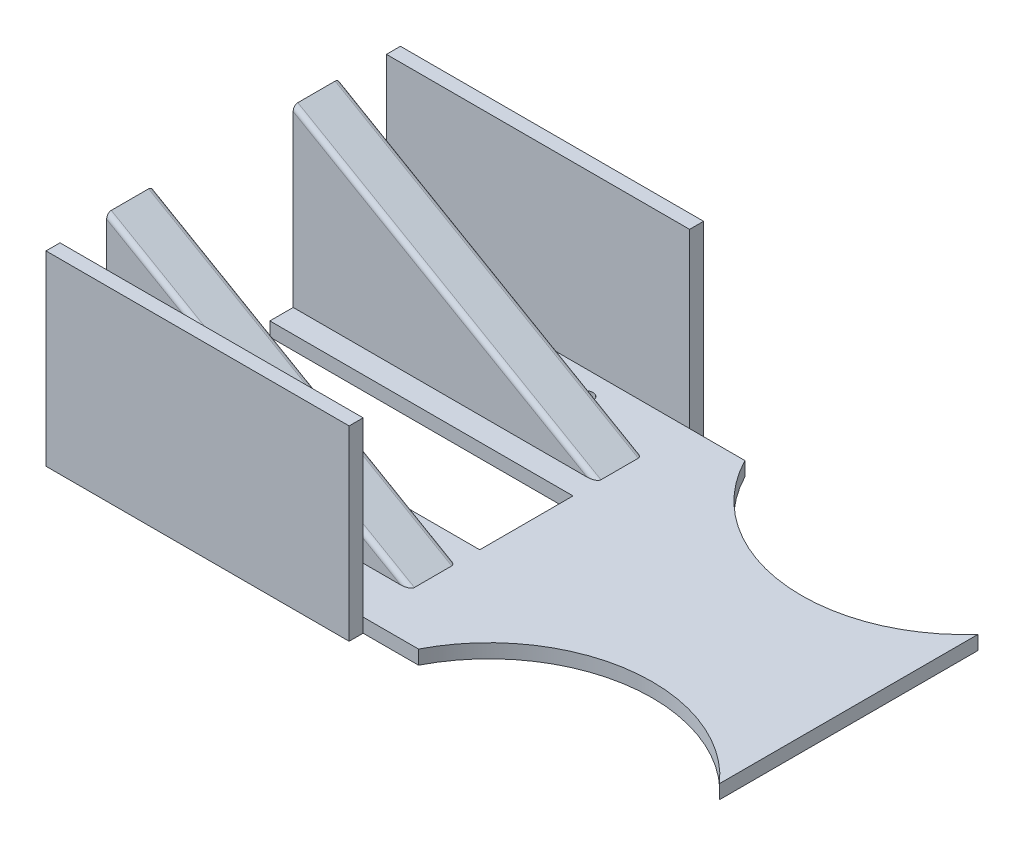
SolidWorks part; units mm, degrees
ref_plane "前视基准面" through (0, 0, 0) normal (0, 0, 1) x (1, 0, 0)
ref_plane "上视基准面" through (0, 0, 0) normal (0, 1, 0) x (1, 0, 0)
ref_plane "右视基准面" through (0, 0, 0) normal (1, 0, 0) x (0, 0, -1)
sketch "草图1" plane through (0, 0, 0) normal (0, 1, 0) x (1, 0, 0)
  line L0 (-92.9537, 0) -> (133.3808, 0) construction
  line L1 (0, 79.573) -> (0, -79.8577) construction
  line L2 (-82.7046, -35) -> (-82.7046, 35)
  line L3 (-82.7046, 35) -> (137.2954, 35)
  line L4 (137.2954, 35) -> (137.2954, -35)
  line L5 (-82.7046, -35) -> (137.2954, -35)
  point P10 (137.2954, 0)
  point P11 (-82.7046, 0)
  dimension "D1" = 70
  dimension "D2" = 220
extrude "凸台-拉伸1" add sketch "草图1" along normal blind 3
sketch "草图2" plane through (0, 0, 0) normal (0, 0, 1) x (1, 0, 0)
  line L0 (-2.7046, 3) -> (-2.7046, 43.2178) construction
  line L2 (59.2954, 3) -> (59.2954, 47.8617) construction
  line L3 (-82.7046, 3) -> (-82.7046, 0) construction
  line L5 (-82.7046, 40.5278) -> (-82.7046, 3)
  line L10 (-82.7046, 3) -> (-17.7046, 3)
  line L11 (-82.7046, 40.5278) -> (-17.7046, 3)
  dimension "D1" = 62
  dimension "D2" = 80
  dimension "D3" = 30
  dimension "D4" = 65
extrude "凸台-拉伸2" add sketch "草图2" along normal blind 25 and the other way blind 25
sketch "草图6" plane through (-82.7046, 0, 0) normal (-1, 0, 0) x (0, 0, 1)
  line L0 (0, 40.5278) -> (0, 0) construction
  line L1 (-25, 40.5278) -> (25, 40.5278) construction
  line L2 (-15, 40.5278) -> (-15, 3)
  line L3 (-15, 3) -> (15, 3)
  line L4 (15, 3) -> (15, 40.5278)
  line L5 (15, 40.5278) -> (-15, 40.5278)
  dimension "D1" = 15
  dimension "D2" = 15
extrude "切除-拉伸4" cut sketch "草图6" against normal through all
ref_plane "基准面1" through (-87.2964, 23.391, 0) normal (-0.9659, 0.2588, 0) x (0, 0, 1)
sketch "草图7" plane through (0, 3, 0) normal (0, 1, 0) x (1, 0, 0)
  line L0 (-2.7046, 35) -> (-2.7046, -35) construction
  line L4 (137.2954, 35) -> (-82.7046, 35) construction
  line L5 (-82.7046, -35) -> (137.2954, -35) construction
  line L6 (-82.7046, 35) -> (-82.7046, 25) construction
  line L7 (53.2954, 35) -> (53.2954, -35) construction
  line L8 (25.2954, 88.1076) -> (25.2954, -100.7895) construction
  line L9 (-82.7046, 0) -> (117.2954, 0) construction
  line L11 (-82.7046, 15) -> (-82.7046, -15) construction
  circle A0 centre (25.2954, 51) radius 35
  circle A1 centre (25.2954, -51) radius 35
  dimension "D4" = 70
  dimension "D1" = 80
  dimension "D2" = 56
  dimension "D3" = 28
  dimension "D5" = 102
extrude "切除-拉伸5" cut sketch "草图7" against normal through all
sketch "草图8" plane through (-82.7046, 0, 0) normal (-1, 0, 0) x (0, 0, 1)
  line L0 (35, 0) -> (35, 40)
  line L1 (35, 40) -> (38, 40)
  line L2 (38, 40) -> (38, 0)
  line L3 (38, 0) -> (35, 0)
  line L4 (0, 36.5043) -> (0, -13.2047) construction
  line L5 (-38, 0) -> (-35, 0)
  line L6 (-38, 40) -> (-38, 0)
  line L7 (-35, 40) -> (-38, 40)
  line L8 (-35, 0) -> (-35, 40)
  dimension "D1" = 3
  dimension "D2" = 40
extrude "凸台-拉伸3" add sketch "草图8" against normal blind 65
sketch "草图9" plane through (0, 3, 0) normal (0, 1, 0) x (1, 0, 0)
  line L0 (-82.7046, 15) -> (-82.7046, -15) construction
  line L1 (-82.7046, 0) -> (117.2954, 0) construction
  circle A0 centre (-74.7668, 29.8601) radius 1.5
  circle A1 centre (-54.7668, 29.8601) radius 1.5
  circle A2 centre (-34.7668, 29.8601) radius 1.5
  circle A3 centre (-34.7668, -29.8601) radius 1.5
  circle A4 centre (-54.7668, -29.8601) radius 1.5
  circle A5 centre (-74.7668, -29.8601) radius 1.5
  circle A12 centre (68.0316, 22) radius 1.5
  circle A13 centre (88.0316, 22) radius 1.5
  circle A14 centre (108.0316, 22) radius 1.5
  circle A15 centre (108.0316, -22) radius 1.5
  circle A16 centre (88.0316, -22) radius 1.5
  circle A17 centre (68.0316, -22) radius 1.5
  circle A18 centre (128.0316, 22) radius 1.5
  circle A19 centre (128.0316, -22) radius 1.5
  dimension "D1" = 3
  dimension "D3" = 22
  dimension "D5" = 3
  dimension "D7" = 3
  dimension "D9" = 3
  dimension "D4" = 20
  dimension "D8" = 20
  dimension "D2" = 3
  dimension "D6" = 3
extrude "切除-拉伸6" cut sketch "草图9" against normal through all
fillet "圆角5" radius 1 4 edges at (-50.2046, 21.7639, -15) (-50.2046, 21.7639, 15) (-50.2046, 21.7639, 25) (-50.2046, 21.7639, -25)
sketch "草图10" plane through (0, 3, 0) normal (0, 1, 0) x (1, 0, 0)
  line L0 (-82.7046, 0) -> (137.2954, 0) construction
  line L1 (-82.7046, 15) -> (-82.7046, -15) construction
  line L2 (137.2954, 35) -> (137.2954, -35) construction
  line L3 (-82.7046, -10) -> (-82.7046, 10)
  line L4 (-82.7046, 10) -> (-17.7046, 10)
  line L5 (-17.7046, 10) -> (-17.7046, -10)
  line L6 (-82.7046, -10) -> (-17.7046, -10)
  point P11 (-17.7046, 0)
  dimension "D1" = 20
extrude "切除-拉伸7" cut sketch "草图10" against normal through all
sketch "草图11" plane through (0, 0, 0) normal (0, 1, 0) x (1, 0, 0)
  line L0 (-17.7046, 10) -> (-17.7046, -10)
  line L1 (-17.7046, -10) -> (114.778, -10)
  line L2 (114.778, -10) -> (114.778, 10)
  line L3 (114.778, 10) -> (-17.7046, 10)
sketch "草图12" plane through (0, 3, 0) normal (0, 1, 0) x (1, 0, 0)
  line L2 (51.4241, 0) -> (51.4241, 45.1417)
  line L3 (51.4241, 45.1417) -> (51.4241, -42.9308)
  line L6 (51.4241, 45.1417) -> (162.1112, 35)
  line L7 (162.1112, 35) -> (165.9627, -47.0392)
  line L8 (165.9627, -47.0392) -> (51.4241, -42.9308)
  arc M13 (-5.8334, -35) -> (56.4241, -35) centre (25.2954, -51) cw
  line M14 (56.4241, -35) -> (137.2954, -35)
  line M15 (137.2954, -35) -> (137.2954, 35)
  line M16 (137.2954, 35) -> (56.4241, 35)
  arc M17 (56.4241, 35) -> (-5.8334, 35) centre (25.2954, 51) cw
  circle M27 centre (68.0316, 22) radius 1.5
  circle M28 centre (128.0316, -22) radius 1.5
  circle M32 centre (128.0316, 22) radius 1.5
  circle M35 centre (88.0316, 22) radius 1.5
  circle M36 centre (108.0316, 22) radius 1.5
  circle M37 centre (108.0316, -22) radius 1.5
  circle M38 centre (88.0316, -22) radius 1.5
  circle M39 centre (68.0316, -22) radius 1.5
extrude "切除-拉伸8" cut sketch "草图12" against normal through all contours L2 L3 M13 M14 M15 M16 M17 M28 M32 M36 M38 M39 M37 M35 M27
